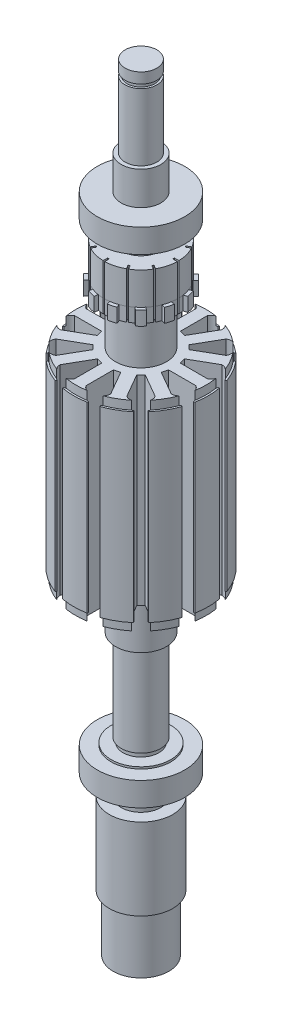
SolidWorks part; units mm, degrees
material "AISI 1020"
ref_plane "Alzado" through (0, 0, 0) normal (0, 0, 1) x (1, 0, 0)
ref_plane "Planta" through (0, 0, 0) normal (0, 1, 0) x (1, 0, 0)
ref_plane "Vista lateral" through (0, 0, 0) normal (1, 0, 0) x (0, 0, -1)
sketch "Croquis1" plane through (0, 0, 0) normal (0, 0, 1) x (1, 0, 0)
  line L0 (0, 138.48) -> (0, -61.52) construction
  line L1 (0, 101.4605) -> (-4, 101.4605)
  line L2 (-4, 101.4605) -> (-4, 98.8105)
  line L3 (-4, 98.8105) -> (-3.5, 98.8105)
  line L4 (-3.5, 98.8105) -> (-3.5, 97.8105)
  line L5 (-3.5, 97.8105) -> (-4, 97.8105)
  line L6 (-4, 97.8105) -> (-4, 80.9605)
  line L7 (-4, 80.9605) -> (-5, 80.9605)
  line L8 (-5, 80.9605) -> (-5, 65.5605) construction
  line L9 (-5, 65.5605) -> (-4.5, 65.5605)
  line L10 (-4.5, 65.5605) -> (-4.5, 64.3605)
  line L11 (-4.5, 64.3605) -> (-5, 64.3605)
  line L12 (-5, 64.3605) -> (-5, 62.0605)
  line L13 (-5, 62.0605) -> (-9.35, 62.0605)
  line L14 (-9.35, 62.0605) -> (-9.35, 53.9105)
  line L15 (-9.35, 53.9105) -> (-10.25, 53.9105)
  line L16 (-10.25, 53.9105) -> (-10.25, 50.4105)
  line L17 (-10.25, 50.4105) -> (-6.4, 50.4105)
  line L18 (-6.4, 50.4105) -> (-6.4, 38.6105)
  line L19 (-6.4, 38.6105) -> (-16.45, 38.6105)
  line L21 (-16.45, -11.6895) -> (-6.4, -11.6895)
  line L22 (-6.4, -11.6895) -> (-6.4, -23.4895)
  line L23 (-6.4, -23.4895) -> (-5, -23.4895)
  line L24 (-5, -23.4895) -> (-5, -46.3895)
  line L25 (-5, -46.3895) -> (-4.5, -46.3895)
  line L26 (-4.5, -46.3895) -> (-4.5, -47.5895)
  line L27 (-4.5, -47.5895) -> (-5, -47.5895)
  line L30 (0, -76.3626) -> (0, 101.4605)
  line L31 (-16.45, 38.6105) -> (-16.45, 36.4605)
  line L32 (-16.45, 36.4605) -> (-16.925, 36.4605)
  line L33 (-16.925, 36.4605) -> (-16.925, -9.5395)
  line L34 (-16.925, -9.5395) -> (-16.45, -9.5395)
  line L35 (-16.45, -9.5395) -> (-16.45, -11.6895)
  line L36 (-5, -47.5895) -> (-7.5, -47.5895)
  line L37 (-7.5, -47.5895) -> (-7.5, -48.0895)
  line L38 (-7.5, -48.0895) -> (-11, -48.0895)
  line L39 (-11, -48.0895) -> (-11, -54.0895)
  line L40 (-11, -54.0895) -> (-5, -54.0895)
  line L41 (-5, -54.0895) -> (-5, -59.2895)
  line L42 (-5, -59.2895) -> (-8, -59.2895)
  line L43 (-8, -59.2895) -> (-8, -79.7895)
  line L44 (-8, -79.7895) -> (-7.0167, -79.7895)
  line L45 (-7.0167, -79.7895) -> (-7.0167, -93.9895)
  line L46 (-7.0167, -93.9895) -> (-6.6241, -93.9895)
  line L47 (-6.6241, -93.9895) -> (-2.2829, -76.3626)
  line L48 (-2.2829, -76.3626) -> (0, -76.3626)
  line L49 (0, -76.3626) -> (0, -55.3863)
  line L50 (-5, 65.5605) -> (-8, 65.5605)
  line L51 (-8, 65.5605) -> (-8, 66.5605)
  line L52 (-8, 66.5605) -> (-11, 66.5605)
  line L53 (-11, 66.5605) -> (-11, 72.5605)
  line L54 (-11, 72.5605) -> (-5, 72.5605)
  line L55 (-5, 72.5605) -> (-5, 80.9605)
  point P5 (-16.45, 37.5355)
  point P38 (-16.925, 13.4605)
  dimension "D1" = 4
  dimension "D2" = 3.5
  dimension "D3" = 4
  dimension "D4" = 2.65
  dimension "D5" = 1
  dimension "D6" = 20.5
  dimension "D7" = 5
  dimension "D8" = 1.2
  dimension "D9" = 15.4
  dimension "D10" = 11.65
  dimension "D11" = 2.3
  dimension "D12" = 9.35
  dimension "D13" = 5
  dimension "D14" = 4.5
  dimension "D15" = 10.25
  dimension "D16" = 3.5
  dimension "D17" = 6.4
  dimension "D18" = 6.4
  dimension "D19" = 16.925
  dimension "D20" = 16.45
  dimension "D21" = 50.3
  dimension "D22" = 46
  dimension "D23" = 16.45
  dimension "D24" = 25.15
  dimension "D25" = 11.8
  dimension "D26" = 11.8
  dimension "D27" = 5
  dimension "D28" = 0.5
  dimension "D29" = 1.2
  dimension "D30" = 22.9
  dimension "D31" = 7.5
  dimension "D32" = 6
  dimension "D33" = 11
  dimension "D34" = 5
  dimension "D35" = 5.2
  dimension "D36" = 8
  dimension "D37" = 20.5
  dimension "D38" = 14.2
  dimension "D39" = 4.5
  dimension "D40" = 6
  dimension "D41" = 1
  dimension "D42" = 11
revolve "Revolución1" add sketch "Croquis1" angle 360 about L30
sketch "Croquis2" plane through (0, 62.0605, 0) normal (0, 1, 0) x (1, 0, 0)
  line L0 (0, 0) -> (0, 12.552) construction
  line L1 (-0.2, 11.9983) -> (-0.2, 8.1976)
  line L2 (-0.2, 8.1976) -> (0.2, 8.1976)
  line L3 (0.2, 8.1976) -> (0.2, 11.9983)
  line L4 (4.272, 6.9993) -> (6.1724, 10.2909)
  line L5 (5.826, 10.4909) -> (3.9256, 7.1993)
  line L6 (3.9256, 7.1993) -> (4.272, 6.9993)
  line L7 (7.1993, 3.9256) -> (10.4909, 5.826)
  line L8 (10.2909, 6.1724) -> (6.9993, 4.272)
  line L9 (6.9993, 4.272) -> (7.1993, 3.9256)
  line L10 (8.1976, -0.2) -> (11.9983, -0.2)
  line L11 (11.9983, 0.2) -> (8.1976, 0.2)
  line L12 (8.1976, 0.2) -> (8.1976, -0.2)
  line L13 (6.9993, -4.272) -> (10.2909, -6.1724)
  line L14 (10.4909, -5.826) -> (7.1993, -3.9256)
  line L15 (7.1993, -3.9256) -> (6.9993, -4.272)
  line L16 (3.9256, -7.1993) -> (5.826, -10.4909)
  line L17 (6.1724, -10.2909) -> (4.272, -6.9993)
  line L18 (4.272, -6.9993) -> (3.9256, -7.1993)
  line L19 (-0.2, -8.1976) -> (-0.2, -11.9983)
  line L20 (0.2, -11.9983) -> (0.2, -8.1976)
  line L21 (0.2, -8.1976) -> (-0.2, -8.1976)
  line L22 (-4.272, -6.9993) -> (-6.1724, -10.2909)
  line L23 (-5.826, -10.4909) -> (-3.9256, -7.1993)
  line L24 (-3.9256, -7.1993) -> (-4.272, -6.9993)
  line L25 (-7.1993, -3.9256) -> (-10.4909, -5.826)
  line L26 (-10.2909, -6.1724) -> (-6.9993, -4.272)
  line L27 (-6.9993, -4.272) -> (-7.1993, -3.9256)
  line L28 (-8.1976, 0.2) -> (-11.9983, 0.2)
  line L29 (-11.9983, -0.2) -> (-8.1976, -0.2)
  line L30 (-8.1976, -0.2) -> (-8.1976, 0.2)
  line L31 (-6.9993, 4.272) -> (-10.2909, 6.1724)
  line L32 (-10.4909, 5.826) -> (-7.1993, 3.9256)
  line L33 (-7.1993, 3.9256) -> (-6.9993, 4.272)
  line L34 (-3.9256, 7.1993) -> (-5.826, 10.4909)
  line L35 (-6.1724, 10.2909) -> (-4.272, 6.9993)
  line L36 (-4.272, 6.9993) -> (-3.9256, 7.1993)
  circle A0 centre (0, 0) radius 8.2 construction
  arc A3 (-0.2, 11.9983) -> (0.2, 11.9983) centre (0, 0) cw
  arc A4 (5.826, 10.4909) -> (6.1724, 10.2909) centre (0, 0) cw
  arc A5 (10.2909, 6.1724) -> (10.4909, 5.826) centre (0, 0) cw
  arc A6 (11.9983, 0.2) -> (11.9983, -0.2) centre (0, 0) cw
  arc A7 (10.4909, -5.826) -> (10.2909, -6.1724) centre (0, 0) cw
  arc A8 (6.1724, -10.2909) -> (5.826, -10.4909) centre (0, 0) cw
  arc A9 (0.2, -11.9983) -> (-0.2, -11.9983) centre (0, 0) cw
  arc A10 (-5.826, -10.4909) -> (-6.1724, -10.2909) centre (0, 0) cw
  arc A11 (-10.2909, -6.1724) -> (-10.4909, -5.826) centre (0, 0) cw
  arc A12 (-11.9983, -0.2) -> (-11.9983, 0.2) centre (0, 0) cw
  arc A13 (-10.4909, 5.826) -> (-10.2909, 6.1724) centre (0, 0) cw
  arc A14 (-6.1724, 10.2909) -> (-5.826, 10.4909) centre (0, 0) cw
  point P59 (0, 0)
  dimension "D1" = 16.4
  dimension "D5" = 12
  dimension "D2" = 0.4
  dimension "D3" = 0.2
  dimension "D4" = 12
extrude "Cortar-Extruir1" cut sketch "Croquis2" against normal blind 12
sketch "Croquis4" plane through (0, 53.9105, 0) normal (0, 1, 0) x (1, 0, 0)
  line L0 (0, 0) -> (0, 11.0206) construction
  line L1 (0, 0) -> (3.0413, 11.3503) construction
  line L2 (1.7058, 10.23) -> (1.5644, 9.1555)
  line L3 (1.5644, 9.1555) -> (0.1187, 9.3459)
  line L4 (0.1187, 9.3459) -> (0.1187, 11.707)
  line L5 (0.1187, 11.707) -> (5.9276, 10.3486)
  line L6 (5.9276, 10.3486) -> (4.6488, 8.116)
  line L7 (3.7053, 9.9648) -> (3.3948, 8.637)
  line L8 (3.3948, 8.637) -> (4.6488, 8.116)
  line L9 (4.7758, 8.0344) -> (5.9563, 10.0792)
  line L10 (5.9563, 10.0792) -> (10.3078, 5.9983)
  line L11 (10.3078, 5.9983) -> (8.084, 4.7043)
  line L12 (7.2585, 5.7824) -> (8.084, 4.7043)
  line L13 (8.1913, 6.7771) -> (7.2585, 5.7824)
  line L14 (6.5923, 8.0065) -> (5.9326, 7.1467)
  line L15 (5.9326, 7.1467) -> (4.7758, 8.0344)
  line L16 (8.1531, 4.5701) -> (10.1979, 5.7507)
  line L17 (10.1979, 5.7507) -> (11.926, 0.0408)
  line L18 (11.926, 0.0408) -> (9.3531, 0.032)
  line L19 (9.1772, 1.3785) -> (9.3531, 0.032)
  line L20 (10.4824, 1.7735) -> (9.1772, 1.3785)
  line L21 (9.7124, 3.6377) -> (8.7111, 3.223)
  line L22 (8.7111, 3.223) -> (8.1531, 4.5701)
  line L23 (9.3459, -0.1187) -> (11.707, -0.1187)
  line L24 (11.707, -0.1187) -> (10.3486, -5.9276)
  line L25 (10.3486, -5.9276) -> (8.116, -4.6488)
  line L26 (8.637, -3.3948) -> (8.116, -4.6488)
  line L27 (9.9648, -3.7053) -> (8.637, -3.3948)
  line L28 (10.23, -1.7058) -> (9.1555, -1.5644)
  line L29 (9.1555, -1.5644) -> (9.3459, -0.1187)
  line L30 (8.0344, -4.7758) -> (10.0792, -5.9563)
  line L31 (10.0792, -5.9563) -> (5.9983, -10.3078)
  line L32 (5.9983, -10.3078) -> (4.7043, -8.084)
  line L33 (5.7824, -7.2585) -> (4.7043, -8.084)
  line L34 (6.7771, -8.1913) -> (5.7824, -7.2585)
  line L35 (8.0065, -6.5923) -> (7.1467, -5.9326)
  line L36 (7.1467, -5.9326) -> (8.0344, -4.7758)
  line L37 (4.5701, -8.1531) -> (5.7507, -10.1979)
  line L38 (5.7507, -10.1979) -> (0.0408, -11.926)
  line L39 (0.0408, -11.926) -> (0.032, -9.3531)
  line L40 (1.3785, -9.1772) -> (0.032, -9.3531)
  line L41 (1.7735, -10.4824) -> (1.3785, -9.1772)
  line L42 (3.6377, -9.7124) -> (3.223, -8.7111)
  line L43 (3.223, -8.7111) -> (4.5701, -8.1531)
  line L44 (-0.1187, -9.3459) -> (-0.1187, -11.707)
  line L45 (-0.1187, -11.707) -> (-5.9276, -10.3486)
  line L46 (-5.9276, -10.3486) -> (-4.6488, -8.116)
  line L47 (-3.3948, -8.637) -> (-4.6488, -8.116)
  line L48 (-3.7053, -9.9648) -> (-3.3948, -8.637)
  line L49 (-1.7058, -10.23) -> (-1.5644, -9.1555)
  line L50 (-1.5644, -9.1555) -> (-0.1187, -9.3459)
  line L51 (-4.7758, -8.0344) -> (-5.9563, -10.0792)
  line L52 (-5.9563, -10.0792) -> (-10.3078, -5.9983)
  line L53 (-10.3078, -5.9983) -> (-8.084, -4.7043)
  line L54 (-7.2585, -5.7824) -> (-8.084, -4.7043)
  line L55 (-8.1913, -6.7771) -> (-7.2585, -5.7824)
  line L56 (-6.5923, -8.0065) -> (-5.9326, -7.1467)
  line L57 (-5.9326, -7.1467) -> (-4.7758, -8.0344)
  line L58 (-8.1531, -4.5701) -> (-10.1979, -5.7507)
  line L59 (-10.1979, -5.7507) -> (-11.926, -0.0408)
  line L60 (-11.926, -0.0408) -> (-9.3531, -0.032)
  line L61 (-9.1772, -1.3785) -> (-9.3531, -0.032)
  line L62 (-10.4824, -1.7735) -> (-9.1772, -1.3785)
  line L63 (-9.7124, -3.6377) -> (-8.7111, -3.223)
  line L64 (-8.7111, -3.223) -> (-8.1531, -4.5701)
  line L65 (-9.3459, 0.1187) -> (-11.707, 0.1187)
  line L66 (-11.707, 0.1187) -> (-10.3486, 5.9276)
  line L67 (-10.3486, 5.9276) -> (-8.116, 4.6488)
  line L68 (-8.637, 3.3948) -> (-8.116, 4.6488)
  line L69 (-9.9648, 3.7053) -> (-8.637, 3.3948)
  line L70 (-10.23, 1.7058) -> (-9.1555, 1.5644)
  line L71 (-9.1555, 1.5644) -> (-9.3459, 0.1187)
  line L72 (-8.0344, 4.7758) -> (-10.0792, 5.9563)
  line L73 (-10.0792, 5.9563) -> (-5.9983, 10.3078)
  line L74 (-5.9983, 10.3078) -> (-4.7043, 8.084)
  line L75 (-5.7824, 7.2585) -> (-4.7043, 8.084)
  line L76 (-6.7771, 8.1913) -> (-5.7824, 7.2585)
  line L77 (-8.0065, 6.5923) -> (-7.1467, 5.9326)
  line L78 (-7.1467, 5.9326) -> (-8.0344, 4.7758)
  line L79 (-4.5701, 8.1531) -> (-5.7507, 10.1979)
  line L80 (-5.7507, 10.1979) -> (-0.0408, 11.926)
  line L81 (-0.0408, 11.926) -> (-0.032, 9.3531)
  line L82 (-1.3785, 9.1772) -> (-0.032, 9.3531)
  line L83 (-1.7735, 10.4824) -> (-1.3785, 9.1772)
  line L84 (-3.6377, 9.7124) -> (-3.223, 8.7111)
  line L85 (-3.223, 8.7111) -> (-4.5701, 8.1531)
  arc A0 (6.5923, 8.0065) -> (8.1913, 6.7771) centre (6.8119, 6.6376) cw
  arc A1 (1.7058, 10.23) -> (3.7053, 9.9648) centre (2.5805, 9.1543) cw
  arc A2 (9.7124, 3.6377) -> (10.4824, 1.7735) centre (9.2181, 2.3424) cw
  arc A3 (10.23, -1.7058) -> (9.9648, -3.7053) centre (9.1543, -2.5805) cw
  arc A4 (8.0065, -6.5923) -> (6.7771, -8.1913) centre (6.6376, -6.8119) cw
  arc A5 (3.6377, -9.7124) -> (1.7735, -10.4824) centre (2.3424, -9.2181) cw
  arc A6 (-1.7058, -10.23) -> (-3.7053, -9.9648) centre (-2.5805, -9.1543) cw
  arc A7 (-6.5923, -8.0065) -> (-8.1913, -6.7771) centre (-6.8119, -6.6376) cw
  arc A8 (-9.7124, -3.6377) -> (-10.4824, -1.7735) centre (-9.2181, -2.3424) cw
  arc A9 (-10.23, 1.7058) -> (-9.9648, 3.7053) centre (-9.1543, 2.5805) cw
  arc A10 (-8.0065, 6.5923) -> (-6.7771, 8.1913) centre (-6.6376, 6.8119) cw
  arc A11 (-3.6377, 9.7124) -> (-1.7735, 10.4824) centre (-2.3424, 9.2181) cw
  point P115 (0, 0)
  dimension "D1" = 1
  dimension "D2" = 1
  dimension "D3" = 7.5
  dimension "D4" = 13.162
  dimension "D5" = 12
extrude "Cortar-Extruir9" cut sketch "Croquis4" against normal up to next
sketch "Croquis5" plane through (0, 38.6105, 0) normal (0, 1, 0) x (1, 0, 0)
  line L0 (0, 0) -> (0, 20.831) construction
  line L1 (0, 0) -> (0, 20.8058) construction
  line L2 (3.1, 16.6387) -> (3.0571, 16.3222) construction
  line L3 (2.936, 8.0417) -> (6.3644, 13.9799) construction
  line L4 (1.4782, 8.4323) -> (1.4782, 15.2891) construction
  line L5 (-3.1, 16.6387) -> (-3.0571, 16.3222) construction
  line L6 (-1.4782, 8.4323) -> (-1.4782, 15.2891) construction
  line L7 (5.6347, 15.9595) -> (5.5136, 15.6639) construction
  line L8 (11.004, 12.8595) -> (10.8086, 12.6069) construction
  line L9 (5.4963, 6.5635) -> (8.9247, 12.5017) construction
  line L10 (6.5635, 5.4963) -> (12.5017, 8.9247) construction
  line L11 (12.8595, 11.004) -> (12.6069, 10.8086) construction
  line L12 (15.9595, 5.6347) -> (15.6639, 5.5136) construction
  line L13 (8.0417, 2.936) -> (13.9799, 6.3644) construction
  line L14 (8.4323, 1.4782) -> (15.2891, 1.4782) construction
  line L15 (16.6387, 3.1) -> (16.3222, 3.0571) construction
  line L16 (16.6387, -3.1) -> (16.3222, -3.0571) construction
  line L17 (8.4323, -1.4782) -> (15.2891, -1.4782) construction
  line L18 (8.0417, -2.936) -> (13.9799, -6.3644) construction
  line L19 (15.9595, -5.6347) -> (15.6639, -5.5136) construction
  line L20 (12.8595, -11.004) -> (12.6069, -10.8086) construction
  line L21 (6.5635, -5.4963) -> (12.5017, -8.9247) construction
  line L22 (5.4963, -6.5635) -> (8.9247, -12.5017) construction
  line L23 (11.004, -12.8595) -> (10.8086, -12.6069) construction
  line L24 (5.6347, -15.9595) -> (5.5136, -15.6639) construction
  line L25 (2.936, -8.0417) -> (6.3644, -13.9799) construction
  line L26 (1.4782, -8.4323) -> (1.4782, -15.2891) construction
  line L27 (3.1, -16.6387) -> (3.0571, -16.3222) construction
  line L28 (-3.1, -16.6387) -> (-3.0571, -16.3222) construction
  line L29 (-1.4782, -8.4323) -> (-1.4782, -15.2891) construction
  line L30 (-2.936, -8.0417) -> (-6.3644, -13.9799) construction
  line L31 (-5.6347, -15.9595) -> (-5.5136, -15.6639) construction
  line L32 (-11.004, -12.8595) -> (-10.8086, -12.6069) construction
  line L33 (-5.4963, -6.5635) -> (-8.9247, -12.5017) construction
  line L34 (-6.5635, -5.4963) -> (-12.5017, -8.9247) construction
  line L35 (-12.8595, -11.004) -> (-12.6069, -10.8086) construction
  line L36 (-15.9595, -5.6347) -> (-15.6639, -5.5136) construction
  line L37 (-8.0417, -2.936) -> (-13.9799, -6.3644) construction
  line L38 (-8.4323, -1.4782) -> (-15.2891, -1.4782) construction
  line L39 (-16.6387, -3.1) -> (-16.3222, -3.0571) construction
  line L40 (-16.6387, 3.1) -> (-16.3222, 3.0571) construction
  line L41 (-8.4323, 1.4782) -> (-15.2891, 1.4782) construction
  line L42 (-8.0417, 2.936) -> (-13.9799, 6.3644) construction
  line L43 (-15.9595, 5.6347) -> (-15.6639, 5.5136) construction
  line L44 (-12.8595, 11.004) -> (-12.6069, 10.8086) construction
  line L45 (-6.5635, 5.4963) -> (-12.5017, 8.9247) construction
  line L46 (-5.4963, 6.5635) -> (-8.9247, 12.5017) construction
  line L47 (-11.004, 12.8595) -> (-10.8086, 12.6069) construction
  line L48 (-5.6347, 15.9595) -> (-5.5136, 15.6639) construction
  line L49 (-2.936, 8.0417) -> (-6.3644, 13.9799) construction
  line L50 (1.4782, 8.4323) -> (2.936, 8.0417)
  line L51 (2.936, 8.0417) -> (6.3644, 13.9799)
  line L52 (1.4782, 8.4323) -> (1.4782, 15.2891)
  line L53 (3.0571, 16.3222) -> (3.1, 16.6387)
  line L54 (3.1, 16.6387) -> (3.3025, 16.7928)
  line L55 (5.5136, 15.6639) -> (5.6347, 15.9595)
  line L56 (5.6347, 15.9595) -> (5.5136, 16.2486)
  line L57 (5.5136, 16.2486) -> (3.3025, 16.7928)
  line L58 (5.4963, 6.5635) -> (8.9247, 12.5017)
  line L59 (10.8086, 12.6069) -> (11.004, 12.8595)
  line L60 (11.004, 12.8595) -> (11.2564, 12.8917)
  line L61 (12.8992, 11.3149) -> (11.2564, 12.8917)
  line L62 (12.8595, 11.004) -> (12.8992, 11.3149)
  line L63 (12.6069, 10.8086) -> (12.8595, 11.004)
  line L64 (6.5635, 5.4963) -> (12.5017, 8.9247)
  line L65 (5.4963, 6.5635) -> (6.5635, 5.4963)
  line L66 (8.0417, 2.936) -> (13.9799, 6.3644)
  line L67 (15.6639, 5.5136) -> (15.9595, 5.6347)
  line L68 (15.9595, 5.6347) -> (16.1942, 5.5364)
  line L69 (16.8285, 3.3494) -> (16.1942, 5.5364)
  line L70 (16.6387, 3.1) -> (16.8285, 3.3494)
  line L71 (16.3222, 3.0571) -> (16.6387, 3.1)
  line L72 (8.4323, 1.4782) -> (15.2891, 1.4782)
  line L73 (8.0417, 2.936) -> (8.4323, 1.4782)
  line L74 (8.4323, -1.4782) -> (15.2891, -1.4782)
  line L75 (16.3222, -3.0571) -> (16.6387, -3.1)
  line L76 (16.6387, -3.1) -> (16.7928, -3.3025)
  line L77 (16.2486, -5.5136) -> (16.7928, -3.3025)
  line L78 (15.9595, -5.6347) -> (16.2486, -5.5136)
  line L79 (15.6639, -5.5136) -> (15.9595, -5.6347)
  line L80 (8.0417, -2.936) -> (13.9799, -6.3644)
  line L81 (8.4323, -1.4782) -> (8.0417, -2.936)
  line L82 (6.5635, -5.4963) -> (12.5017, -8.9247)
  line L83 (12.6069, -10.8086) -> (12.8595, -11.004)
  line L84 (12.8595, -11.004) -> (12.8917, -11.2564)
  line L85 (11.3149, -12.8992) -> (12.8917, -11.2564)
  line L86 (11.004, -12.8595) -> (11.3149, -12.8992)
  line L87 (10.8086, -12.6069) -> (11.004, -12.8595)
  line L88 (5.4963, -6.5635) -> (8.9247, -12.5017)
  line L89 (6.5635, -5.4963) -> (5.4963, -6.5635)
  line L90 (2.936, -8.0417) -> (6.3644, -13.9799)
  line L91 (5.5136, -15.6639) -> (5.6347, -15.9595)
  line L92 (5.6347, -15.9595) -> (5.5364, -16.1942)
  line L93 (3.3494, -16.8285) -> (5.5364, -16.1942)
  line L94 (3.1, -16.6387) -> (3.3494, -16.8285)
  line L95 (3.0571, -16.3222) -> (3.1, -16.6387)
  line L96 (1.4782, -8.4323) -> (1.4782, -15.2891)
  line L97 (2.936, -8.0417) -> (1.4782, -8.4323)
  line L98 (-1.4782, -8.4323) -> (-1.4782, -15.2891)
  line L99 (-3.0571, -16.3222) -> (-3.1, -16.6387)
  line L100 (-3.1, -16.6387) -> (-3.3025, -16.7928)
  line L101 (-5.5136, -16.2486) -> (-3.3025, -16.7928)
  line L102 (-5.6347, -15.9595) -> (-5.5136, -16.2486)
  line L103 (-5.5136, -15.6639) -> (-5.6347, -15.9595)
  line L104 (-2.936, -8.0417) -> (-6.3644, -13.9799)
  line L105 (-1.4782, -8.4323) -> (-2.936, -8.0417)
  line L106 (-5.4963, -6.5635) -> (-8.9247, -12.5017)
  line L107 (-10.8086, -12.6069) -> (-11.004, -12.8595)
  line L108 (-11.004, -12.8595) -> (-11.2564, -12.8917)
  line L109 (-12.8992, -11.3149) -> (-11.2564, -12.8917)
  line L110 (-12.8595, -11.004) -> (-12.8992, -11.3149)
  line L111 (-12.6069, -10.8086) -> (-12.8595, -11.004)
  line L112 (-6.5635, -5.4963) -> (-12.5017, -8.9247)
  line L113 (-5.4963, -6.5635) -> (-6.5635, -5.4963)
  line L114 (-8.0417, -2.936) -> (-13.9799, -6.3644)
  line L115 (-15.6639, -5.5136) -> (-15.9595, -5.6347)
  line L116 (-15.9595, -5.6347) -> (-16.1942, -5.5364)
  line L117 (-16.8285, -3.3494) -> (-16.1942, -5.5364)
  line L118 (-16.6387, -3.1) -> (-16.8285, -3.3494)
  line L119 (-16.3222, -3.0571) -> (-16.6387, -3.1)
  line L120 (-8.4323, -1.4782) -> (-15.2891, -1.4782)
  line L121 (-8.0417, -2.936) -> (-8.4323, -1.4782)
  line L122 (-8.4323, 1.4782) -> (-15.2891, 1.4782)
  line L123 (-16.3222, 3.0571) -> (-16.6387, 3.1)
  line L124 (-16.6387, 3.1) -> (-16.7928, 3.3025)
  line L125 (-16.2486, 5.5136) -> (-16.7928, 3.3025)
  line L126 (-15.9595, 5.6347) -> (-16.2486, 5.5136)
  line L127 (-15.6639, 5.5136) -> (-15.9595, 5.6347)
  line L128 (-8.0417, 2.936) -> (-13.9799, 6.3644)
  line L129 (-8.4323, 1.4782) -> (-8.0417, 2.936)
  line L130 (-6.5635, 5.4963) -> (-12.5017, 8.9247)
  line L131 (-12.6069, 10.8086) -> (-12.8595, 11.004)
  line L132 (-12.8595, 11.004) -> (-12.8917, 11.2564)
  line L133 (-11.3149, 12.8992) -> (-12.8917, 11.2564)
  line L134 (-11.004, 12.8595) -> (-11.3149, 12.8992)
  line L135 (-10.8086, 12.6069) -> (-11.004, 12.8595)
  line L136 (-5.4963, 6.5635) -> (-8.9247, 12.5017)
  line L137 (-6.5635, 5.4963) -> (-5.4963, 6.5635)
  line L138 (-2.936, 8.0417) -> (-6.3644, 13.9799)
  line L139 (-5.5136, 15.6639) -> (-5.6347, 15.9595)
  line L140 (-5.6347, 15.9595) -> (-5.5364, 16.1942)
  line L141 (-3.3494, 16.8285) -> (-5.5364, 16.1942)
  line L142 (-3.1, 16.6387) -> (-3.3494, 16.8285)
  line L143 (-3.0571, 16.3222) -> (-3.1, 16.6387)
  line L144 (-1.4782, 8.4323) -> (-1.4782, 15.2891)
  line L145 (-2.936, 8.0417) -> (-1.4782, 8.4323)
  arc A0 (-3.1, 16.6387) -> (3.1, 16.6387) centre (0, 0) cw construction
  circle A1 centre (0, 0) radius 16.925 construction
  arc A2 (1.4782, 15.2891) -> (3.0571, 16.3222) centre (3.2288, 14.3366) cw construction
  arc A3 (-1.4782, 15.2891) -> (-3.0571, 16.3222) centre (-3.2288, 14.3366) ccw construction
  arc A4 (6.3644, 13.9799) -> (5.5136, 15.6639) centre (4.3721, 14.0303) ccw construction
  arc A5 (5.6347, 15.9595) -> (11.004, 12.8595) centre (0, 0) cw construction
  arc A6 (8.9247, 12.5017) -> (10.8086, 12.6069) centre (9.9645, 10.8015) cw construction
  arc A7 (12.5017, 8.9247) -> (12.6069, 10.8086) centre (10.8015, 9.9645) ccw construction
  arc A8 (12.8595, 11.004) -> (15.9595, 5.6347) centre (0, 0) cw construction
  arc A9 (13.9799, 6.3644) -> (15.6639, 5.5136) centre (14.0303, 4.3721) cw construction
  arc A10 (15.2891, 1.4782) -> (16.3222, 3.0571) centre (14.3366, 3.2288) ccw construction
  arc A11 (16.6387, 3.1) -> (16.6387, -3.1) centre (0, 0) cw construction
  arc A12 (15.2891, -1.4782) -> (16.3222, -3.0571) centre (14.3366, -3.2288) cw construction
  arc A13 (13.9799, -6.3644) -> (15.6639, -5.5136) centre (14.0303, -4.3721) ccw construction
  arc A14 (15.9595, -5.6347) -> (12.8595, -11.004) centre (0, 0) cw construction
  arc A15 (12.5017, -8.9247) -> (12.6069, -10.8086) centre (10.8015, -9.9645) cw construction
  arc A16 (8.9247, -12.5017) -> (10.8086, -12.6069) centre (9.9645, -10.8015) ccw construction
  arc A17 (11.004, -12.8595) -> (5.6347, -15.9595) centre (0, 0) cw construction
  arc A18 (6.3644, -13.9799) -> (5.5136, -15.6639) centre (4.3721, -14.0303) cw construction
  arc A19 (1.4782, -15.2891) -> (3.0571, -16.3222) centre (3.2288, -14.3366) ccw construction
  arc A20 (3.1, -16.6387) -> (-3.1, -16.6387) centre (0, 0) cw construction
  arc A21 (-1.4782, -15.2891) -> (-3.0571, -16.3222) centre (-3.2288, -14.3366) cw construction
  arc A22 (-6.3644, -13.9799) -> (-5.5136, -15.6639) centre (-4.3721, -14.0303) ccw construction
  arc A23 (-5.6347, -15.9595) -> (-11.004, -12.8595) centre (0, 0) cw construction
  arc A24 (-8.9247, -12.5017) -> (-10.8086, -12.6069) centre (-9.9645, -10.8015) cw construction
  arc A25 (-12.5017, -8.9247) -> (-12.6069, -10.8086) centre (-10.8015, -9.9645) ccw construction
  arc A26 (-12.8595, -11.004) -> (-15.9595, -5.6347) centre (0, 0) cw construction
  arc A27 (-13.9799, -6.3644) -> (-15.6639, -5.5136) centre (-14.0303, -4.3721) cw construction
  arc A28 (-15.2891, -1.4782) -> (-16.3222, -3.0571) centre (-14.3366, -3.2288) ccw construction
  arc A29 (-16.6387, -3.1) -> (-16.6387, 3.1) centre (0, 0) cw construction
  arc A30 (-15.2891, 1.4782) -> (-16.3222, 3.0571) centre (-14.3366, 3.2288) cw construction
  arc A31 (-13.9799, 6.3644) -> (-15.6639, 5.5136) centre (-14.0303, 4.3721) ccw construction
  arc A32 (-15.9595, 5.6347) -> (-12.8595, 11.004) centre (0, 0) cw construction
  arc A33 (-12.5017, 8.9247) -> (-12.6069, 10.8086) centre (-10.8015, 9.9645) cw construction
  arc A34 (-8.9247, 12.5017) -> (-10.8086, 12.6069) centre (-9.9645, 10.8015) ccw construction
  arc A35 (-11.004, 12.8595) -> (-5.6347, 15.9595) centre (0, 0) cw construction
  arc A36 (-6.3644, 13.9799) -> (-5.5136, 15.6639) centre (-4.3721, 14.0303) cw construction
  arc A37 (1.4782, 15.2891) -> (3.0571, 16.3222) centre (3.2288, 14.3366) cw
  arc A38 (5.5136, 15.6639) -> (6.3644, 13.9799) centre (4.3721, 14.0303) cw
  arc A39 (8.9247, 12.5017) -> (10.8086, 12.6069) centre (9.9645, 10.8015) cw
  arc A40 (12.6069, 10.8086) -> (12.5017, 8.9247) centre (10.8015, 9.9645) cw
  arc A41 (13.9799, 6.3644) -> (15.6639, 5.5136) centre (14.0303, 4.3721) cw
  arc A42 (16.3222, 3.0571) -> (15.2891, 1.4782) centre (14.3366, 3.2288) cw
  arc A43 (15.2891, -1.4782) -> (16.3222, -3.0571) centre (14.3366, -3.2288) cw
  arc A44 (15.6639, -5.5136) -> (13.9799, -6.3644) centre (14.0303, -4.3721) cw
  arc A45 (12.5017, -8.9247) -> (12.6069, -10.8086) centre (10.8015, -9.9645) cw
  arc A46 (10.8086, -12.6069) -> (8.9247, -12.5017) centre (9.9645, -10.8015) cw
  arc A47 (6.3644, -13.9799) -> (5.5136, -15.6639) centre (4.3721, -14.0303) cw
  arc A48 (3.0571, -16.3222) -> (1.4782, -15.2891) centre (3.2288, -14.3366) cw
  arc A49 (-1.4782, -15.2891) -> (-3.0571, -16.3222) centre (-3.2288, -14.3366) cw
  arc A50 (-5.5136, -15.6639) -> (-6.3644, -13.9799) centre (-4.3721, -14.0303) cw
  arc A51 (-8.9247, -12.5017) -> (-10.8086, -12.6069) centre (-9.9645, -10.8015) cw
  arc A52 (-12.6069, -10.8086) -> (-12.5017, -8.9247) centre (-10.8015, -9.9645) cw
  arc A53 (-13.9799, -6.3644) -> (-15.6639, -5.5136) centre (-14.0303, -4.3721) cw
  arc A54 (-16.3222, -3.0571) -> (-15.2891, -1.4782) centre (-14.3366, -3.2288) cw
  arc A55 (-15.2891, 1.4782) -> (-16.3222, 3.0571) centre (-14.3366, 3.2288) cw
  arc A56 (-15.6639, 5.5136) -> (-13.9799, 6.3644) centre (-14.0303, 4.3721) cw
  arc A57 (-12.5017, 8.9247) -> (-12.6069, 10.8086) centre (-10.8015, 9.9645) cw
  arc A58 (-10.8086, 12.6069) -> (-8.9247, 12.5017) centre (-9.9645, 10.8015) cw
  arc A59 (-6.3644, 13.9799) -> (-5.5136, 15.6639) centre (-4.3721, 14.0303) cw
  arc A60 (-3.0571, 16.3222) -> (-1.4782, 15.2891) centre (-3.2288, 14.3366) cw
  point P130 (0, 0)
  point P267 (0, 0)
  dimension "D1" = 0
  dimension "D2" = 12
  dimension "D3" = 3.1
  dimension "D4" = 12
extrude "Cortar-Extruir10" cut sketch "Croquis5" against normal up to next
